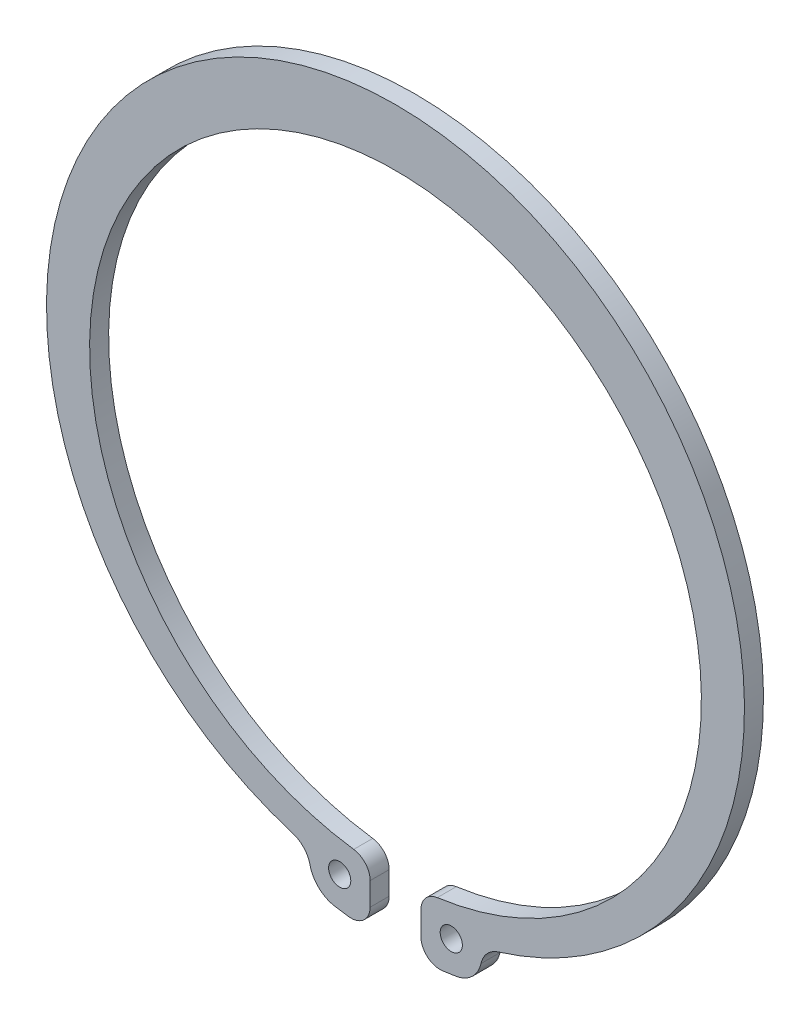
SolidWorks part; units mm, degrees
material "Сталь 14Х17Н2 ГОСТ 5632-72"
ref_plane "Plane1" through (0, 0, 0) normal (0, 0, 1) x (1, 0, 0)
ref_plane "Plane2" through (0, 0, 0) normal (0, 1, 0) x (1, 0, 0)
ref_plane "Plane3" through (0, 0, 0) normal (1, 0, 0) x (0, 0, -1)
sketch "Sketch1" plane through (0, 0, 0) normal (0, 0, 1) x (1, 0, 0)
  line L0 (-9.8681, 2.2) -> (9.8681, 2.2) construction
  line L1 (-4, -50.7697) -> (-4, -54.4015)
  line L2 (0, 0) -> (0, -31.9595) construction
  line L3 (4, -50.7697) -> (4, -54.4015)
  line L4 (-8.8, -53.6714) -> (-8.8, -50.9586) construction
  line L5 (-8.8, -52.315) -> (-8.0038, -47.5815) construction
  line L6 (-8.8, -52.315) -> (-9.5962, -57.0485) construction
  line L7 (-8.8, -52.315) -> (-4, -52.315) construction
  line L8 (0, 57.25) -> (0, 48.25) construction
  arc A0 (6.5902, -47.7978) -> (-6.5902, -47.7978) centre (0, 0) ccw
  arc A1 (4, -50.7697) -> (6.5902, -47.7978) centre (7, -50.7697) cw
  circle A2 centre (-8.8, -52.315) radius 1.75
  arc A3 (-4, -50.7697) -> (-6.5902, -47.7978) centre (-7, -50.7697) ccw
  arc A5 (-13.4848, -53.3605) -> (-9.5962, -57.0485) centre (-8.8, -52.315) ccw
  arc A6 (-13.4848, -53.3605) -> (-16.2108, -50.409) centre (-17.3887, -54.2317) ccw
  arc A7 (-9.5962, -57.0485) -> (-7.3829, -57.377) centre (0, 0) ccw
  arc A8 (-7.3829, -57.377) -> (-4, -54.4015) centre (-7, -54.4015) ccw
  circle A9 centre (8.8, -52.315) radius 1.75
  arc A10 (7.3829, -57.377) -> (4, -54.4015) centre (7, -54.4015) cw
  arc A11 (9.5962, -57.0485) -> (7.3829, -57.377) centre (0, 0) cw
  arc A12 (13.4848, -53.3605) -> (9.5962, -57.0485) centre (8.8, -52.315) cw
  arc A13 (13.4848, -53.3605) -> (16.2108, -50.409) centre (17.3887, -54.2317) cw
  arc A14 (16.2108, -50.409) -> (-16.2108, -50.409) centre (0, 2.2) ccw
  circle A15 centre (0, 0) radius 60.5 construction
  point P4 (0, 2.2)
  point P19 (-4, -48.0839)
  dimension "d4" = 3.5
  dimension "r2" = 3
  dimension "d3" = 110.1
  dimension "corpus" = 121
  dimension "r1" = 4
  dimension "d1" = 96.5
  dimension "e" = 2.2
  dimension "l" = 8
  dimension "a" = 9.6
  dimension "B" = 9
extrude "Extrude1" add sketch "Sketch1" along normal blind 3
sketch "Sketch2" plane through (0, 0, 0) normal (1, 0, 0) x (0, 0, -1)
  line L0 (0, 0) -> (10.3458, 0) construction
  line L3 (-3, 48.25) -> (0.4, 48.25)
  line L4 (-8.3, 50) -> (-8.3, 48)
  line L5 (-8.3, 50) -> (-3, 50)
  line L6 (-3, 50) -> (-3, 48.25)
  line L7 (-3, 57.25) -> (-3, -50.409) construction
  line L8 (0.4, 48.25) -> (0.4, 50)
  dimension "D1" = 2
  dimension "m" = 3.4
  dimension "h" = 5.3
  dimension "D2" = 96.5
  dimension "d" = 100
